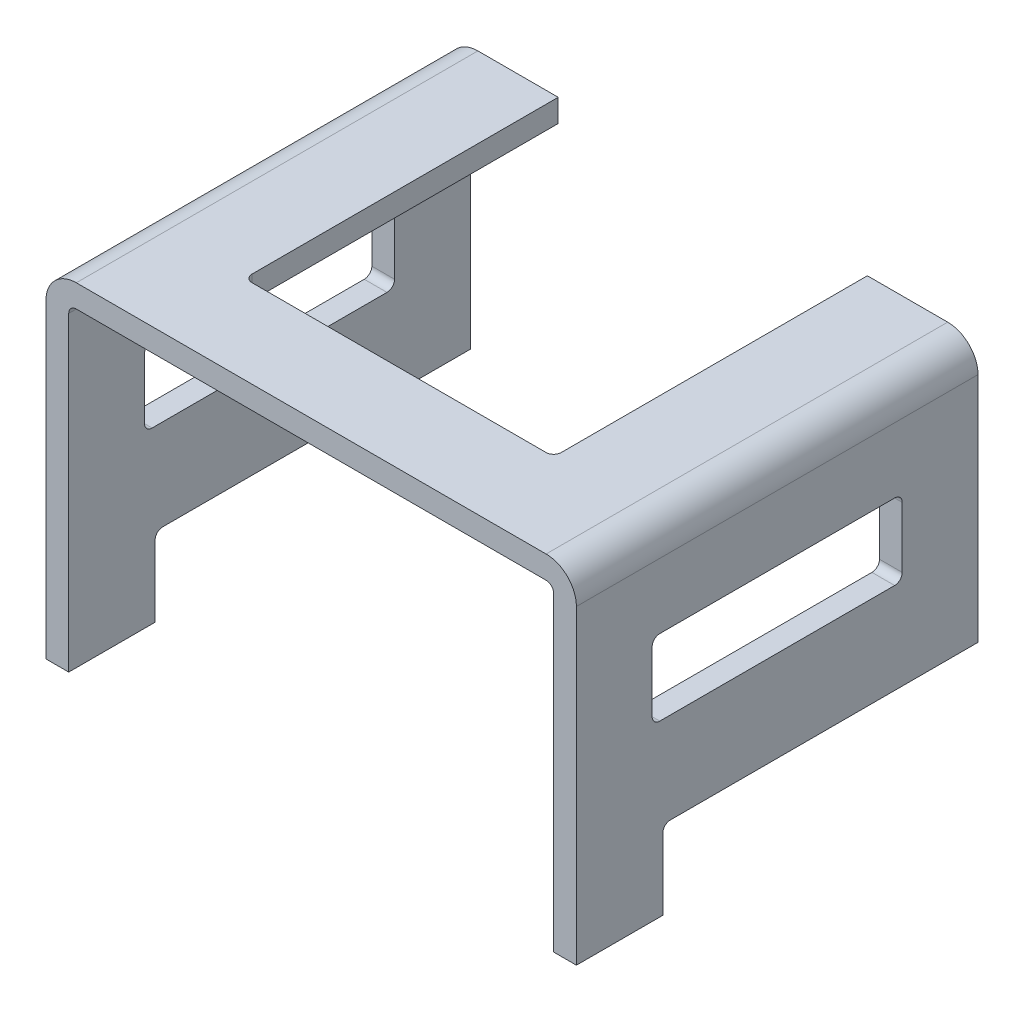
SolidWorks part; units mm, degrees
ref_plane "Front Plane" through (0, 0, 0) normal (0, 0, 1) x (1, 0, 0)
ref_plane "Top Plane" through (0, 0, 0) normal (0, 1, 0) x (1, 0, 0)
ref_plane "Right Plane" through (0, 0, 0) normal (1, 0, 0) x (0, 0, -1)
ref_plane "Plane1" through (0, 14, 0) normal (0, 1, 0) x (1, 0, 0)
sketch "Sketch1" plane through (0, 14, 0) normal (0, 1, 0) x (1, 0, 0)
  line L0 (17.5, -16) -> (17.5, 10.5)
  line L1 (17.5, 10.5) -> (-17.5, 10.5)
  line L2 (-17.5, 10.5) -> (-17.5, -16)
  line L3 (-17.5, -16) -> (17.5, -16)
extrude "Boss-Extrude1" add sketch "Sketch1" against normal blind 22.5
sketch "Sketch2" plane through (0, 0, 16) normal (0, 0, 1) x (1, 0, 0)
  line L0 (16, -8.5) -> (16, 12.5)
  line L1 (16, 12.5) -> (-16, 12.5)
  line L2 (-16, 12.5) -> (-16, -8.5)
  line L3 (-16, -8.5) -> (16, -8.5)
extrude "Cut-Extrude1" cut sketch "Sketch2" against normal through all
sketch "Sketch3" plane through (16, 0, 0) normal (-1, 0, 0) x (0, 0, 1)
  line L0 (10.3, -3.3) -> (-10.5, -3.3)
  line L1 (-10.5, -3.3) -> (-10.5, -8.5)
  line L2 (-10.5, -8.5) -> (10.3, -8.5)
  line L3 (10.3, -8.5) -> (10.3, -3.3)
extrude "Cut-Extrude2" cut sketch "Sketch3" against normal through all
sketch "Sketch4" plane through (0, 12.5, 0) normal (0, -1, 0) x (1, 0, 0)
  line L0 (-10.2, -10.5) -> (10.2, -10.5)
  line L1 (10.2, -10.5) -> (10.2, 10.2)
  line L2 (10.2, 10.2) -> (-10.2, 10.2)
  line L3 (-10.2, 10.2) -> (-10.2, -10.5)
extrude "Cut-Extrude3" cut sketch "Sketch4" against normal through all
sketch "Sketch5" plane through (-16, 0, 0) normal (1, 0, 0) x (0, 0, -1)
  line L0 (-10.3, -3.3) -> (-10.3, -8.5)
  line L1 (-10.3, -8.5) -> (10.5, -8.5)
  line L2 (10.5, -8.5) -> (10.5, -3.3)
  line L3 (10.5, -3.3) -> (-10.3, -3.3)
extrude "Cut-Extrude4" cut sketch "Sketch5" against normal through all
fillet "Fillet1" radius 0.5 2 edges at (-16, 12.5, 2.75) (16, 12.5, 2.75)
fillet "Fillet2" radius 2 2 edges at (-17.5, 14, 2.75) (17.5, 14, 2.75)
sketch "Sketch6" plane through (17.5, 0, 0) normal (1, 0, 0) x (0, 0, -1)
  line L0 (-10.3, -3.3) -> (10.5, -3.3) construction
  line L1 (-11, 7.7) -> (5.5, 7.7)
  line L2 (-11, 7.7) -> (-11, 2.7)
  line L3 (-11, 2.7) -> (5.5, 2.7)
  line L4 (5.5, 7.7) -> (5.5, 2.7)
  line L5 (-16, -8.5) -> (-16, 12) construction
  dimension "D1" = 5
  dimension "D2" = 6
  dimension "D3" = 16.5
  dimension "D4" = 5
extrude "Cut-Extrude5" cut sketch "Sketch6" against normal blind 35
fillet "Fillet3" radius 0.5 12 edges at (-16.75, 2.7, 11) (16.75, 2.7, -5.5) (-16.75, 2.7, -5.5) (16.75, 7.7, -5.5) (-16.75, 7.7, -5.5) (16.75, 7.7, 11) (-16.75, 7.7, 11) (-16.75, -3.3, 10.3) (10.2, 13.25, 10.2) (-10.2, 13.25, 10.2) (16.75, -3.3, 10.3) (16.75, 2.7, 11)
